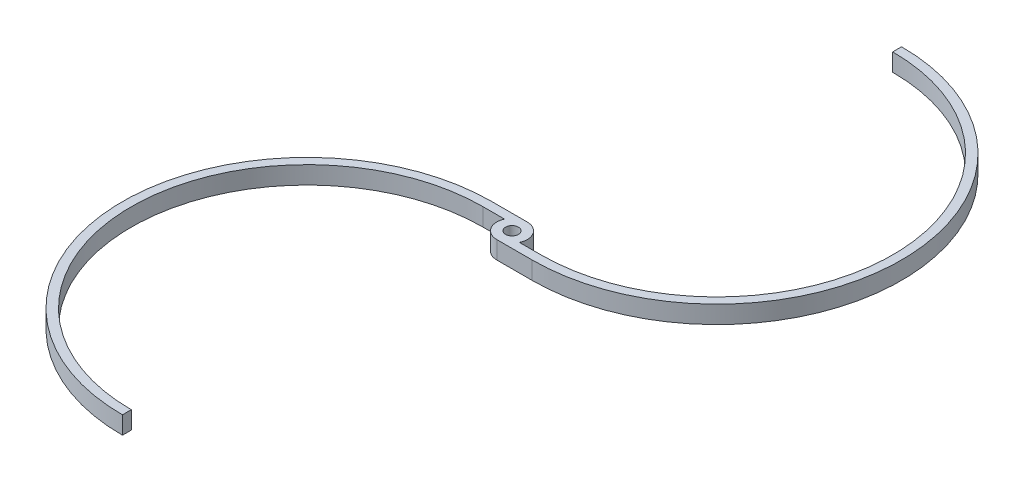
SolidWorks part; units mm, degrees
ref_plane "Front Plane" through (0, 0, 0) normal (0, 0, 1) x (1, 0, 0)
ref_plane "Top Plane" through (0, 0, 0) normal (0, 1, 0) x (1, 0, 0)
ref_plane "Right Plane" through (0, 0, 0) normal (1, 0, 0) x (0, 0, -1)
sketch "Sketch1" plane through (0, 0, 0) normal (0, 1, 0) x (1, 0, 0)
  line L0 (-721.8983, 0) -> (1125.3783, 0) construction
  line L1 (0, 765.0267) -> (0, -558.1175) construction
  line L2 (19.5256, -9) -> (50, -9)
  line L3 (0, -21.5) -> (50, -21.5)
  line L5 (50, 487.5) -> (50, 500)
  line L6 (-19.5256, 9) -> (-50, 9)
  line L7 (0, 21.5) -> (-50, 21.5)
  line L9 (-50, -487.5) -> (-50, -500)
  line L11 (50, 239.25) -> (50, -21.5) construction
  line L14 (0, -9) -> (50, -9) construction
  circle A0 centre (0, 0) radius 9
  arc A1 (50, -9) -> (50, 487.5) centre (50, 239.25) ccw
  arc A2 (50, -21.5) -> (50, 500) centre (50, 239.25) ccw
  arc A3 (-50, 9) -> (-50, -487.5) centre (-50, -239.25) ccw
  arc A4 (-50, 21.5) -> (-50, -500) centre (-50, -239.25) ccw
  arc A5 (-19.5256, 9) -> (0, -21.5) centre (0, 0) ccw
  arc A6 (19.5256, -9) -> (0, 21.5) centre (0, 0) ccw
  dimension "D1" = 18
  dimension "D2" = 50
  dimension "D3" = 260.75
  dimension "D6" = 43
  dimension "D7" = 180
  dimension "D8" = 523.8914
  dimension "D9" = 1000
  dimension "D4" = 12.5
  dimension "D5" = 2
extrude "Boss-Extrude1" add sketch "Sketch1" along normal blind 25
